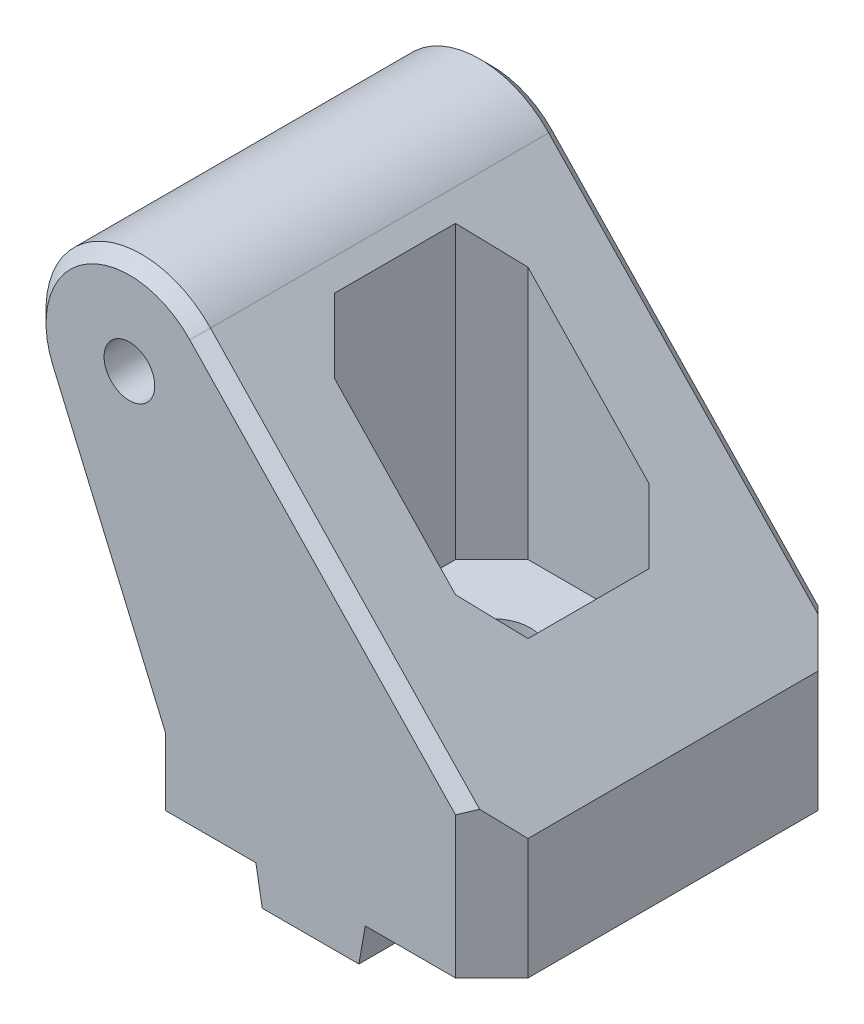
SolidWorks part; units mm, degrees
ref_plane "Alzado" through (0, 0, 0) normal (0, 0, 1) x (1, 0, 0)
ref_plane "Planta" through (0, 0, 0) normal (0, 1, 0) x (1, 0, 0)
ref_plane "Vista lateral" through (0, 0, 0) normal (1, 0, 0) x (0, 0, -1)
sketch "Croquis1" plane through (0, 0, 0) normal (0, 0, 1) x (1, 0, 0)
  line L0 (0, 0) -> (-30, 0) construction
  line L1 (-30, 0) -> (-30, 10)
  line L2 (-30, 10) -> (0, 10) construction
  line L3 (0, 10) -> (0, 0)
  line L7 (-15, 0) -> (-15, 50000) construction
  line L8 (-10.471, 0) -> (-11, -3)
  line L9 (-19, -3) -> (-11, -3)
  line L10 (-19, -3) -> (-19.529, 0)
  line L11 (-10.471, 0) -> (0, 0)
  line L12 (-19.529, 0) -> (-30, 0)
  line L13 (-37.2576, 26.8795) -> (-30, 10)
  line L14 (-24.2841, 35.4533) -> (0, 10)
  circle A0 centre (-30, 30) radius 2.1
  arc A1 (-37.2576, 26.8795) -> (-24.2841, 35.4533) centre (-30, 30) cw
  point P5 (0, 0)
  point P10 (-15, 0)
  point P13 (-15, -3)
  point P18 (-33.7705, 37.949)
  point P19 (-30, 10)
  point P20 (-36.541, 25.57)
  point P21 (-30, 10)
  dimension "D1" = 10
  dimension "D2" = 7.9
  dimension "D3" = 4.2
  dimension "D4" = 30
  dimension "D5" = 3
  dimension "D6" = 8
  dimension "D7" = 80
  dimension "D8" = 15
  dimension "D9" = 30
extrude "Saliente-Extruir1" add sketch "Croquis1" along normal mid plane 30
chamfer "Chaflán1" distance 3 angle 45 4 edges at (-30, 5, 15) (-30, 5, -15) (0, 5, -15) (0, 5, 15)
sketch "Croquis3" plane through (0, 0, 0) normal (0, -1, 0) x (1, 0, 0)
  line L0 (0, 0) -> (-50000, 0) construction
  line L1 (-15, 0) -> (-15, 50000) construction
  line L4 (-7, 8) -> (-23, 8)
  line L5 (-7, 8) -> (-7, -8)
  line L6 (-7, -8) -> (-23, -8)
  line L7 (-23, 8) -> (-23, -8)
  line L8 (-7, 8) -> (-23, -8) construction
  line L9 (-7, -8) -> (-23, 8) construction
  point P7 (-15, 0)
  dimension "D2" = 16
  dimension "D3" = 16
extrude "Cortar-Extruir1" cut sketch "Croquis3" against normal through all from offset 10 offset against normal yes
chamfer "Chaflán2" distance 3 angle 45 4 edges at (-23, 22.0537, 8) (-7, 13.6685, 8) (-7, 13.6685, -8) (-23, 22.0537, -8)
sketch "Croquis4" plane through (0, 10, 0) normal (0, 1, 0) x (1, 0, 0)
  circle A0 centre (-15, 0) radius 3.2
  dimension "D1" = 6.4
extrude "Cortar-Extruir2" cut sketch "Croquis4" against normal through all
sketch "Croquis5" plane through (0, 0, 0) normal (0, -1, 0) x (1, 0, 0)
  line L1 (-20, -5) -> (-10, -5)
  line L2 (-20, -5) -> (-20, 5)
  line L3 (-20, 5) -> (-10, 5)
  line L4 (-10, -5) -> (-10, 5)
  line L5 (-20, -5) -> (-10, 5) construction
  line L6 (-20, 5) -> (-10, -5) construction
  point P0 (-15, 0)
  dimension "D1" = 10
extrude "Cortar-Extruir3" cut sketch "Croquis5" along normal through all
chamfer "Chaflán3" distance 2.5 angle 45 2 edges at (-15, -3, -5) (-15, -3, 5)
chamfer "Chaflán4" distance 1 angle 45 6 edges at (-13.6421, 24.2989, -15) (-32.1288, 14.9511, -15) (-34.3557, 36.5908, -15) (-13.6421, 24.2989, 15) (-34.3557, 36.5908, 15) (-32.1288, 14.9511, 15)
